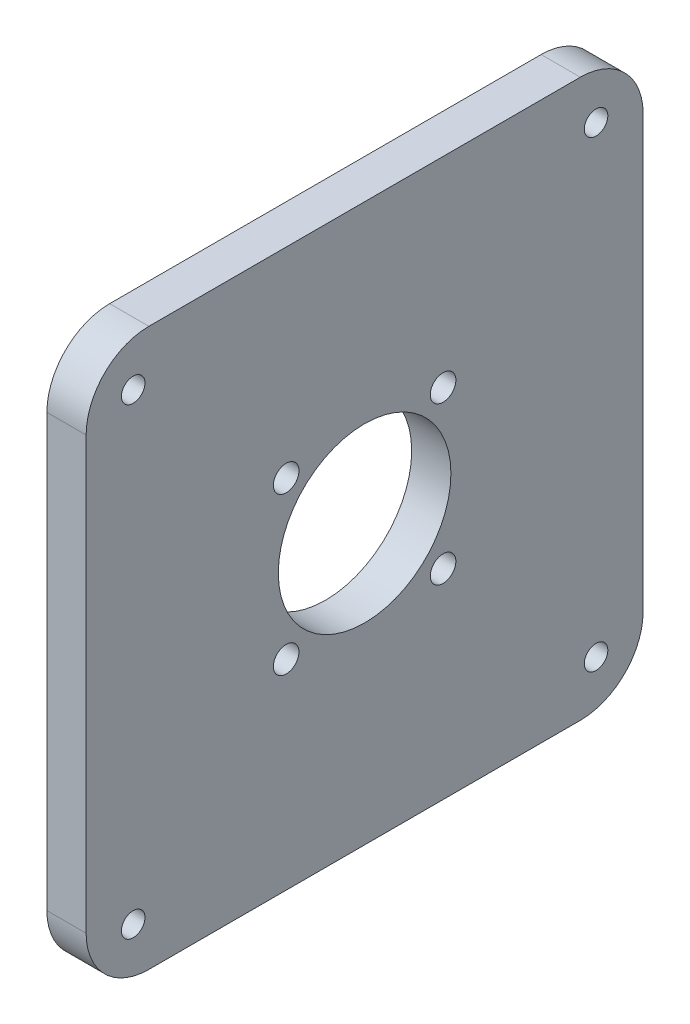
SolidWorks part; units mm, degrees
ref_plane "Front Plane" through (0, 0, 0) normal (0, 0, 1) x (1, 0, 0)
ref_plane "Top Plane" through (0, 0, 0) normal (0, 1, 0) x (1, 0, 0)
ref_plane "Right Plane" through (0, 0, 0) normal (1, 0, 0) x (0, 0, -1)
sketch "Sketch1" plane through (0, 0, 0) normal (1, 0, 0) x (0, 0, -1)
  line L0 (35.5, 71) -> (35.5, 0) construction
  line L1 (0, 0) -> (71, 0)
  line L2 (0, 0) -> (0, 71)
  line L3 (0, 71) -> (71, 71)
  line L4 (71, 0) -> (71, 71)
  line L5 (0, 35.5) -> (71, 35.5) construction
  circle A0 centre (6, 6) radius 1.5
  circle A1 centre (6, 65) radius 1.5
  circle A2 centre (65, 65) radius 1.5
  circle A3 centre (65, 6) radius 1.5
  circle A4 centre (35.5, 35.5) radius 11
  circle A5 centre (25.5, 45.5) radius 1.632
  circle A6 centre (45.5, 45.5) radius 1.632
  circle A7 centre (25.5, 25.5) radius 1.632
  circle A8 centre (45.5, 25.5) radius 1.632
  dimension "D6" = 3
  dimension "D8" = 22
  dimension "D1" = 71
  dimension "D2" = 71
  dimension "D3" = 6
  dimension "D4" = 6
  dimension "D5" = 6
  dimension "D7" = 6
  dimension "D9" = 20
  dimension "D10" = 20
  dimension "D11" = 10
  dimension "D12" = 10
extrude "Boss-Extrude1" add sketch "Sketch1" along normal blind 5
fillet "Fillet1" radius 8 4 edges at (2.5, 0, -71) (2.5, 0, 0) (2.5, 71, -71) (2.5, 71, 0)
